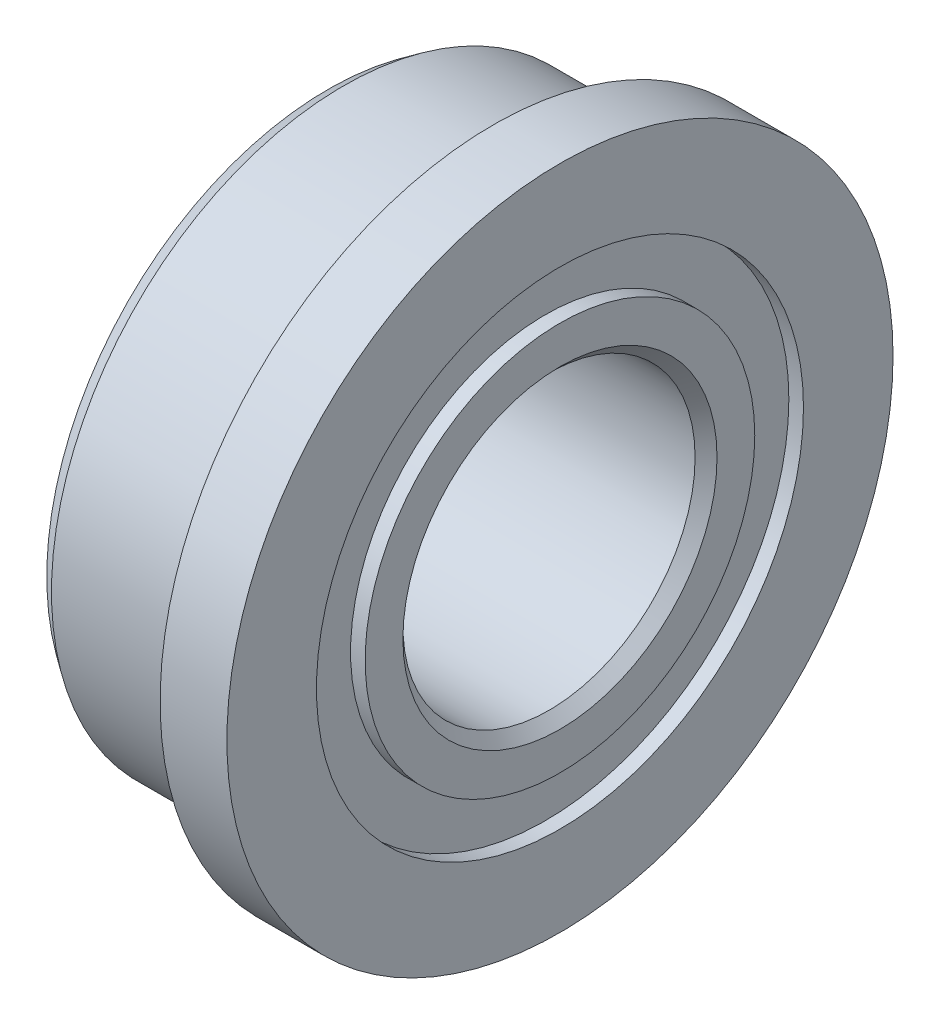
SolidWorks part; units mm, degrees
material "AISI 304"
ref_plane "Piano frontale" through (0, 0, 0) normal (0, 0, 1) x (1, 0, 0)
ref_plane "Piano superiore" through (0, 0, 0) normal (0, 1, 0) x (1, 0, 0)
ref_plane "Piano destro" through (0, 0, 0) normal (1, 0, 0) x (0, 0, -1)
sketch "Schizzo1" plane through (0, 0, 0) normal (0, 0, 1) x (1, 0, 0)
  line L0 (-2.9111, 3.3333) -> (-2.9111, 2.6667)
  line L1 (-2.9111, 2.6667) -> (-3.1751, 2.6667)
  line L2 (-3.1751, 2.6667) -> (-3.1751, 2.1501)
  line L3 (-3.1751, 2.1501) -> (-2.9611, 2)
  line L4 (-2.9611, 2) -> (-0.15, 2)
  line L5 (-0.15, 2) -> (-0.0001, 2.1501)
  line L6 (-0.0001, 2.1501) -> (-0.0001, 2.6667)
  line L7 (-0.0001, 2.6667) -> (-0.2, 2.6667)
  line L8 (-0.2, 2.6667) -> (-0.2, 3.3333)
  line L9 (-0.2, 3.3333) -> (-0.0001, 3.3333)
  line L10 (-0.0001, 3.3333) -> (-0.0001, 4.5595)
  line L11 (-0.0001, 4.5595) -> (-0.9141, 4.5595)
  line L12 (-0.9141, 4.5595) -> (-0.9141, 4.02)
  line L13 (-0.9341, 4) -> (-2.961, 4)
  line L14 (-2.961, 4) -> (-3.1751, 3.8501)
  line L15 (-3.1751, 3.8501) -> (-3.1751, 3.3333)
  line L16 (-3.1751, 3.3333) -> (-2.9111, 3.3333)
  line L17 (-4, 0) -> (0, 0) construction
  arc A0 (-0.9141, 4.02) -> (-0.9341, 4) centre (-0.9141, 4) cw
  dimension "D4" = 2
  dimension "D6" = 0.914
  dimension "D8" = 0.2121
  dimension "D5" = 3.175
  dimension "D9" = 0.264
  dimension "D10" = 0.2613
  dimension "D11" = 0.2613
  dimension "D2" = 2
  dimension "D3" = 0.6667
  dimension "D7" = 0.6667
  dimension "D12" = 125
  dimension "D13" = 125.056
  dimension "D14" = 4.5595
revolve "Rivoluzione1" add sketch "Schizzo1" angle 360 about L17
equation "\"D3@Schizzo1\"=\"D2@Schizzo1\"/3"
equation "\"D7@Schizzo1\"=\"D2@Schizzo1\"/3"
equation "\"D14@Schizzo1\"=9.119/2"
